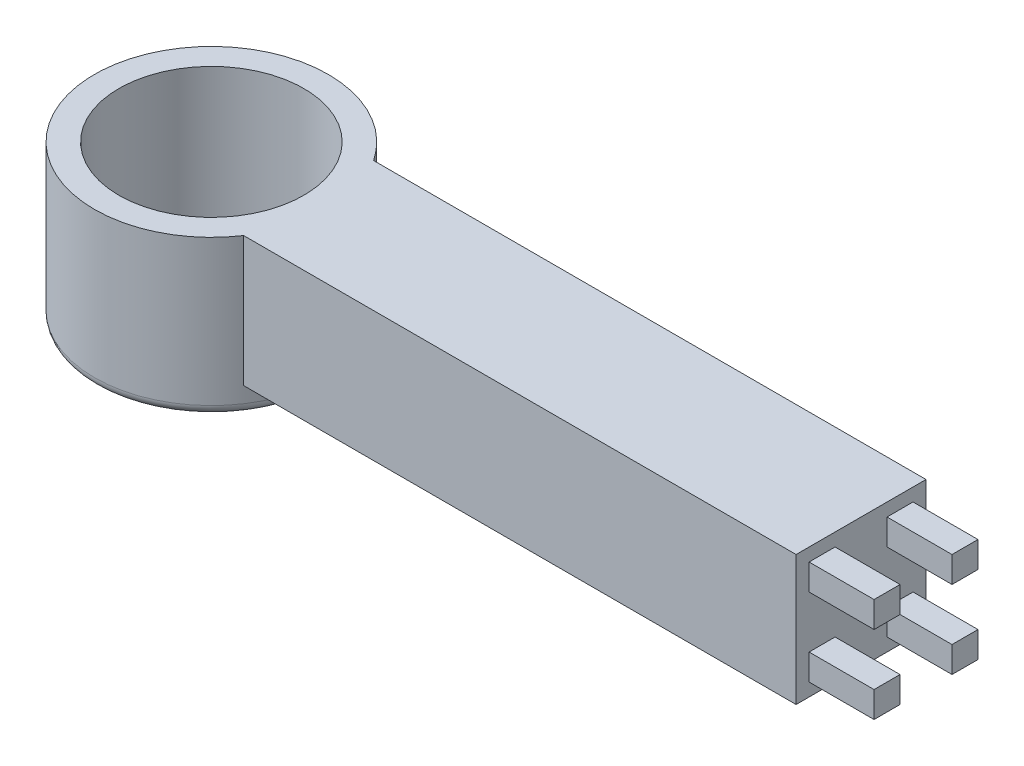
SolidWorks part; units mm, degrees
ref_plane "Front Plane" through (0, 0, 0) normal (0, 0, 1) x (1, 0, 0)
ref_plane "Top Plane" through (0, 0, 0) normal (0, 1, 0) x (1, 0, 0)
ref_plane "Right Plane" through (0, 0, 0) normal (1, 0, 0) x (0, 0, -1)
sketch "Sketch2" plane through (0, 0, 0) normal (0, 0, 1) x (1, 0, 0)
  line L1 (0, 0) -> (635, 0)
  line L2 (0, 0) -> (0, 127)
  line L3 (0, 127) -> (635, 127)
  line L4 (635, 0) -> (635, 127)
  dimension "D1" = 635
  dimension "D2" = 127
extrude "Boss-Extrude1" add sketch "Sketch2" along normal blind 127
sketch "Sketch3" plane through (0, 127, 0) normal (0, 1, 0) x (1, 0, 0)
  line L0 (0, -127) -> (0, 0) construction
  circle A0 centre (0, -63.5) radius 90.424
  circle A1 centre (0, -63.5) radius 114.3
  dimension "D1" = 180.848
  dimension "D2" = 228.6
extrude "Boss-Extrude2" add sketch "Sketch3" against normal blind 152.4
sketch "Sketch4" plane through (0, 127, 0) normal (0, 1, 0) x (1, 0, 0)
  line L0 (0, -127) -> (0, 0) construction
  circle A0 centre (0, -63.5) radius 90.424
  dimension "D1" = 180.848
extrude "Cut-Extrude2" cut sketch "Sketch4" against normal through all both and the other way through all
sketch "Sketch5" plane through (635, 0, 0) normal (1, 0, 0) x (0, 0, -1)
  line L0 (-127, 127) -> (0, 127) construction
  line L3 (-127, 127) -> (-127, 0) construction
  line L6 (-127, 0) -> (0, 0) construction
  line L7 (-114.3, 88.9) -> (-88.9, 88.9)
  line L8 (-114.3, 88.9) -> (-114.3, 114.3)
  line L9 (-114.3, 114.3) -> (-88.9, 114.3)
  line L10 (-88.9, 88.9) -> (-88.9, 114.3)
  line L11 (0, 0) -> (0, 127) construction
  line L12 (-12.7, 12.7) -> (-38.1, 12.7)
  line L13 (-114.3, 12.7) -> (-88.9, 12.7)
  line L14 (-114.3, 12.7) -> (-114.3, 38.1)
  line L15 (-114.3, 38.1) -> (-88.9, 38.1)
  line L16 (-88.9, 12.7) -> (-88.9, 38.1)
  line L17 (-12.7, 12.7) -> (-12.7, 38.1)
  line L18 (-12.7, 38.1) -> (-38.1, 38.1)
  line L19 (-38.1, 12.7) -> (-38.1, 38.1)
  line L21 (-12.7, 114.3) -> (-38.1, 114.3)
  line L22 (-12.7, 114.3) -> (-12.7, 88.9)
  line L23 (-12.7, 88.9) -> (-38.1, 88.9)
  line L24 (-38.1, 114.3) -> (-38.1, 88.9)
  dimension "D1" = 25.4
  dimension "D2" = 25.4
  dimension "D3" = 12.7
  dimension "D4" = 12.7
  dimension "D5" = 25.4
  dimension "D6" = 25.4
  dimension "D7" = 12.7
  dimension "D8" = 12.7
  dimension "D9" = 25.4
  dimension "D10" = 25.4
  dimension "D11" = 12.7
  dimension "D12" = 12.7
  dimension "D13" = 12.7
  dimension "D14" = 12.7
  dimension "D15" = 25.4
  dimension "D16" = 25.4
extrude "Boss-Extrude3" add sketch "Sketch5" along normal blind 63.5
fillet "Fillet1" radius 10 2 edges at (0, -25.4, 153.924) (0, -25.4, 177.8)
